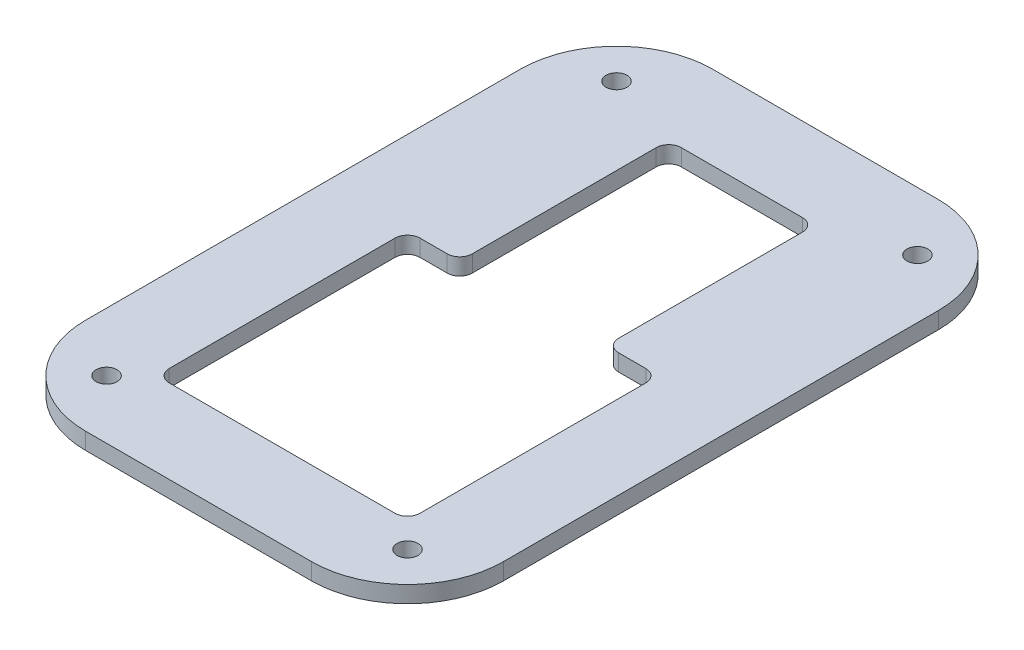
SolidWorks part; units mm, degrees
ref_plane "Front Plane" through (0, 0, 0) normal (0, 0, 1) x (1, 0, 0)
ref_plane "Top Plane" through (0, 0, 0) normal (0, 1, 0) x (1, 0, 0)
ref_plane "Right Plane" through (0, 0, 0) normal (1, 0, 0) x (0, 0, -1)
sketch "Sketch1" plane through (0, 0, 0) normal (0, 1, 0) x (1, 0, 0)
  line L0 (0, -46.4045) -> (0, 54.7714) construction
  line L1 (-27, -30) -> (27, -30)
  line L2 (-30, -27) -> (-30, 27)
  line L3 (-27, 30) -> (-20.5, 30)
  line L4 (30, -27) -> (30, 27)
  line L5 (-30, -30) -> (30, 30) construction
  line L6 (-30, 30) -> (30, -30) construction
  line L7 (-17.5, 33) -> (-17.5, 77)
  line L8 (-14.5, 80) -> (14.5, 80)
  line L9 (17.5, 77) -> (17.5, 33)
  line L10 (20.5, 30) -> (27, 30)
  line L11 (-50, -27) -> (-50, 77)
  line L12 (-27, -50) -> (27, -50)
  line L13 (50, -27) -> (50, 77)
  line L14 (-27, 100) -> (27, 100)
  line L15 (-50, -27) -> (-50, 27) construction
  line L16 (50, -27) -> (50, 27) construction
  line L17 (0, 0) -> (-95.5239, -95.5239) construction
  line L18 (-36, -176.4757) -> (-36, 104.4757) construction
  line L19 (-98.7955, 86) -> (77.6874, 86) construction
  arc A0 (-27, -30) -> (-30, -27) centre (-27, -27) cw
  arc A1 (27, -30) -> (30, -27) centre (27, -27) ccw
  arc A2 (27, 30) -> (30, 27) centre (27, 27) cw
  arc A3 (17.5, 33) -> (20.5, 30) centre (20.5, 33) ccw
  arc A4 (14.5, 80) -> (17.5, 77) centre (14.5, 77) cw
  arc A5 (-17.5, 77) -> (-14.5, 80) centre (-14.5, 77) cw
  arc A6 (-17.5, 33) -> (-20.5, 30) centre (-20.5, 33) cw
  arc A7 (-30, 27) -> (-27, 30) centre (-27, 27) cw
  arc A8 (-27, -50) -> (-50, -27) centre (-27, -27) cw
  arc A9 (27, -50) -> (50, -27) centre (27, -27) ccw
  arc A10 (50, 77) -> (27, 100) centre (27, 77) ccw
  arc A11 (-50, 77) -> (-27, 100) centre (-27, 77) cw
  circle A12 centre (-36, -36) radius 2.5
  circle A13 centre (-36, 86) radius 2.5
  circle A15 centre (36, -36) radius 2.5
  circle A16 centre (36, 86) radius 2.5
  point P0 (0, 0)
  point P23 (17.5, 30)
  dimension "D5" = 3
  dimension "D8" = 23
  dimension "D9" = 5
  dimension "D1" = 60
  dimension "D2" = 60
  dimension "D3" = 35
  dimension "D4" = 50
  dimension "D7" = 20
  dimension "D10" = 14
  dimension "D11" = 14
  dimension "D6" = 20
extrude "Boss-Extrude2" add sketch "Sketch1" along normal blind 4
